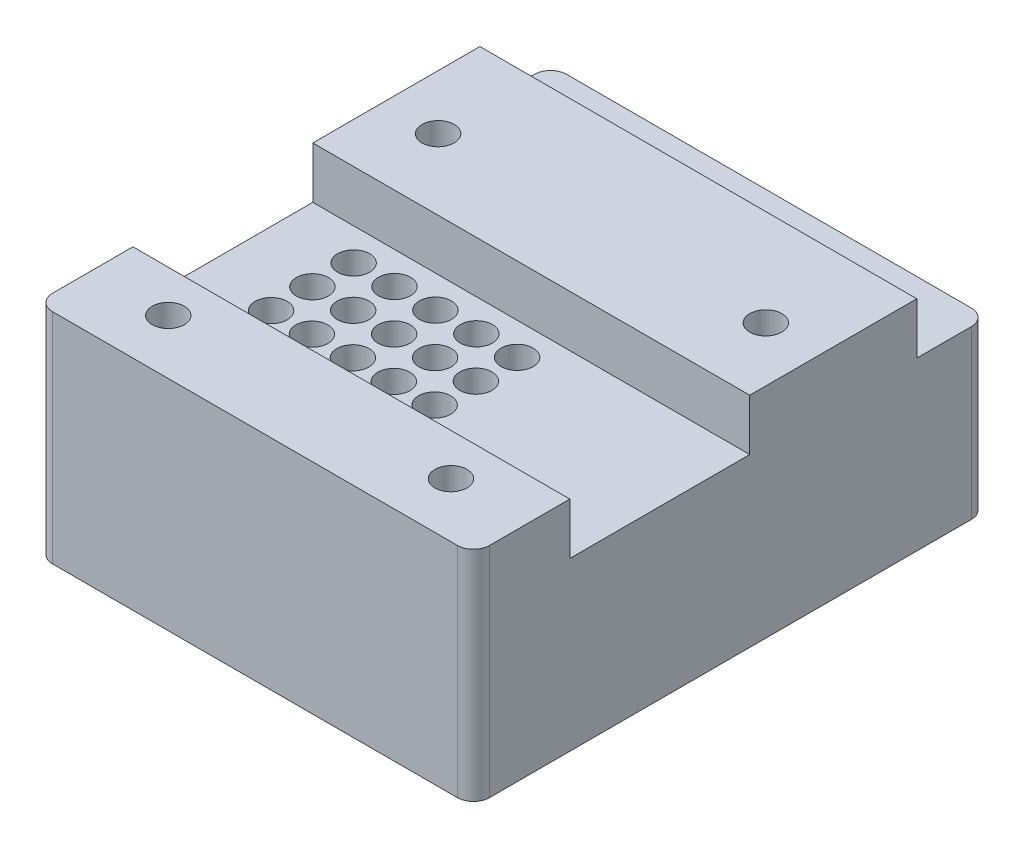
SolidWorks part; units mm, degrees
ref_plane "Front Plane" through (0, 0, 0) normal (0, 0, 1) x (1, 0, 0)
ref_plane "Top Plane" through (0, 0, 0) normal (0, 1, 0) x (1, 0, 0)
ref_plane "Right Plane" through (0, 0, 0) normal (1, 0, 0) x (0, 0, -1)
sketch "Sketch1" plane through (0, 0, 0) normal (0, 1, 0) x (1, 0, 0)
  line L1 (0, 0) -> (68, 0)
  line L2 (0, 0) -> (0, -70)
  line L3 (0, -70) -> (68, -70)
  line L4 (68, 0) -> (68, -70)
  dimension "D1" = 70
  dimension "D2" = 68
extrude "Boss-Extrude2" add sketch "Sketch1" along normal blind 4 contours L2 L1 L4 L3
sketch "Sketch2" plane through (0, 0, 0) normal (0, -1, 0) x (-1, 0, 0)
  line L1 (-34, 0) -> (-34, -70)
  line L2 (0, 0) -> (-68, 0) construction
  line L3 (0, -70) -> (-68, -70) construction
  line L4 (-68, -11) -> (0, -11)
  line L5 (-68, 0) -> (-68, -70) construction
  line L6 (0, 0) -> (0, -70) construction
  line L8 (-54.5, -11) -> (-68, -11)
  line L9 (-54.5, -11) -> (-54.5, -16)
  line L10 (-54.5, -16) -> (-68, -16)
  line L11 (-68, -11) -> (-68, -16)
  line L12 (-13.5, -11) -> (0, -11)
  line L13 (-13.5, -11) -> (-13.5, -16)
  line L14 (-13.5, -16) -> (0, -16)
  line L15 (0, -11) -> (0, -16)
  point P16 (-54.5, -11)
  point P17 (-13.5, -11)
  line M3 (0, -70) -> (0, 0)
  dimension "D1" = 11
  dimension "D2" = 20.5
  dimension "D3" = 20.5
  dimension "D4" = 5
  dimension "D5" = 5
extrude "Boss-Extrude4" add sketch "Sketch2" along normal blind 22 contours L13 L14 L4 M3 | L9 L8 L11 L10
sketch "Sketch3" plane through (0, 0, 11) normal (0, 0, -1) x (-1, 0, 0)
  line L0 (0, 0) -> (-68, 0) construction
  line L1 (-54.5, -22) -> (-54.5, 0) construction
  line L2 (-54.5, 0) -> (-68, 0) construction
  circle A0 centre (-59.07, -14.83) radius 2
  circle A1 centre (-59.07, -4.71) radius 2
  circle A2 centre (-8.93, -14.83) radius 2
  circle A3 centre (-8.93, -4.71) radius 2
  dimension "D1" = 4
  dimension "D2" = 4
  dimension "D3" = 4
  dimension "D4" = 4
  dimension "D5" = 4.71
  dimension "D6" = 4.57
  dimension "D7" = 4.57
  dimension "D8" = 14.83
extrude "Cut-Extrude1" cut sketch "Sketch3" against normal blind 10
sketch "Sketch4" plane through (0, 0, 0) normal (0, -1, 0) x (-1, 0, 0)
  line L0 (0, -42) -> (-68, -42)
  line L1 (0, -16) -> (0, -70) construction
  line L2 (-68, -16) -> (-68, -70) construction
  line L3 (-13.5, -16) -> (0, -16) construction
  line L5 (0, -42) -> (-5, -42)
  line L6 (0, -42) -> (0, -67.69)
  line L7 (0, -67.69) -> (-5, -67.69)
  line L8 (-5, -42) -> (-5, -67.69)
  line L9 (-43.15, -42) -> (-48.15, -42)
  line L10 (-43.15, -42) -> (-43.15, -67.69)
  line L11 (-43.15, -67.69) -> (-48.15, -67.69)
  line L12 (-48.15, -42) -> (-48.15, -67.69)
  line M13 (0, -70) -> (0, -16)
  dimension "D1" = 26
  dimension "D2" = 25.69
  dimension "D3" = 5
  dimension "D4" = 5
  dimension "D5" = 48.15
extrude "Boss-Extrude5" add sketch "Sketch4" along normal blind 15 contours L0 L8 L7 M13 | L0 L12 L11 L10
sketch "Sketch5" plane through (0, -15, 0) normal (0, -1, 0) x (-1, 0, 0)
  line L0 (0, -42) -> (-5, -42) construction
  line L1 (0, -67.69) -> (0, -42) construction
  line L3 (0, -67.69) -> (-5, -67.69) construction
  line L4 (-43.15, -67.69) -> (-48.15, -67.69) construction
  line L5 (-48.15, -42) -> (-48.15, -67.69) construction
  line L6 (-43.15, -42) -> (-48.15, -42) construction
  circle A0 centre (-2.3, -65.24) radius 1.3
  circle A1 centre (-2.3, -44.45) radius 1.3
  circle A2 centre (-45.85, -65.24) radius 1.3
  circle A3 centre (-45.85, -44.45) radius 1.3
  dimension "D1" = 2.6
  dimension "D2" = 2.6
  dimension "D3" = 2.6
  dimension "D4" = 2.6
  dimension "D5" = 2.45
  dimension "D7" = 2.3
  dimension "D8" = 2.45
  dimension "D9" = 2.45
  dimension "D10" = 2.3
  dimension "D11" = 2.45
  dimension "D12" = 2.3
  dimension "D6" = 2.3
extrude "Cut-Extrude2" cut sketch "Sketch5" against normal blind 6
sketch "Sketch6" plane through (0, 0, 70) normal (0, 0, 1) x (1, 0, 0)
  line L1 (0, 4) -> (68, 4)
  line L2 (0, 4) -> (0, 0)
  line L3 (0, 0) -> (68, 0)
  line L4 (68, 4) -> (68, 0)
extrude "Boss-Extrude6" add sketch "Sketch6" along normal blind 10
sketch "Sketch7" plane through (0, 0, 0) normal (0, -1, 0) x (-1, 0, 0)
  line L0 (0, -42) -> (-5, -42) construction
  line L1 (0, -16) -> (-3, -16)
  line L2 (0, -16) -> (0, -42)
  line L3 (0, -42) -> (-3, -42)
  line L4 (-3, -16) -> (-3, -42)
  line L10 (-54.5, -16) -> (-68, -16) construction
  line L19 (-54.5, -11) -> (-68, -11) construction
  line L20 (-65, -11) -> (-68, -11)
  line L21 (-65, -11) -> (-65, 0)
  line L22 (-65, 0) -> (-68, 0)
  line L23 (-68, -11) -> (-68, 0)
  line L24 (0, 0) -> (-68, 0) construction
  line L25 (0, -11) -> (-3, -11)
  line L26 (0, -11) -> (0, 0)
  line L27 (0, 0) -> (-3, 0)
  line L28 (-3, -11) -> (-3, 0)
  line L29 (0, -67.69) -> (-3, -67.69)
  line L30 (-3, 0) -> (-15.1638, 0)
  line L31 (-3, 0) -> (-3, -3)
  line L32 (-3, -3) -> (-15.1638, -3)
  line L33 (-15.1638, 0) -> (-15.1638, -3)
  line L34 (-65, 0) -> (-47.6978, 0)
  line L35 (-65, 0) -> (-65, -3)
  line L36 (-65, -3) -> (-47.6978, -3)
  line L37 (-47.6978, 0) -> (-47.6978, -3)
  line L38 (-3, -77) -> (-59, -77)
  line L39 (-59, -16) -> (-68, -16)
  line L40 (-68, -80) -> (0, -80)
  line L41 (0, -67.69) -> (-3, -67.69)
  line L42 (0, -67.69) -> (-3, -67.69)
  line L43 (-3, -77) -> (-3, -67.69)
  line L44 (0, -67.69) -> (0, -80)
  line L45 (0, -80) -> (-68, -80)
  line L46 (-68, -80) -> (-68, -16)
  line L47 (-59, -16) -> (-59, -77)
  line L48 (0, -67.69) -> (0, -80)
  line M28 (-54.5, -16) -> (-68, -16)
  line M29 (-68, -16) -> (-68, -80)
  line M30 (-68, -80) -> (0, -80)
  line M31 (0, -80) -> (0, -67.69)
  line M32 (0, -67.69) -> (-5, -67.69)
  dimension "D1" = 3
  dimension "D2" = 3
  dimension "D3" = 3
  dimension "D7" = 3
  dimension "D8" = 3
extrude "Boss-Extrude7" add sketch "Sketch7" along normal blind 22 contours L47 L43 L38 M28 M29 M30 M31 M32
sketch "Sketch8" plane through (0, 0, 0) normal (0, -1, 0) x (-1, 0, 0)
  line L0 (-13.5, -16) -> (0, -16) construction
  line L1 (0, -42) -> (-3, -42)
  line L2 (0, -42) -> (0, -16)
  line L3 (0, -16) -> (-3, -16)
  line L4 (-3, -42) -> (-3, -16)
  dimension "D1" = 3
extrude "Boss-Extrude8" add sketch "Sketch8" along normal blind 22
sketch "Sketch9" plane through (0, 0, 0) normal (0, -1, 0) x (1, 0, 0)
  line L5 (68, 11) -> (68, 0)
  line L21 (65, 3) -> (65, 11)
  line L22 (65, 11) -> (68, 11)
  line L23 (0, 11) -> (0, 0)
  line L27 (3, 3) -> (3, 11)
  line L28 (3, 11) -> (0, 11)
  line L29 (3, 3) -> (3, 0)
  line L30 (0, 0) -> (68, 0) construction
  line L31 (3, 0) -> (0, 0)
  line L32 (65, 3) -> (65, 0)
  line L33 (65, 0) -> (68, 0)
  dimension "D3" = 3
extrude "Boss-Extrude9" add sketch "Sketch9" along normal blind 22 contours L27 L28 L23 L31 L29 | L21 L22 L5 L33 L32
sketch "Sketch12" plane through (0, -22, 0) normal (0, -1, 0) x (-1, 0, 0)
  line L0 (-3, -16) -> (-3, -42) construction
  line L1 (0, -42) -> (-3, -42)
  line L2 (0, -42) -> (0, -41)
  line L3 (0, -41) -> (-3, -41)
  line L4 (-3, -42) -> (-3, -41)
  line L5 (-3, -77) -> (-3, -67.69) construction
  line L6 (0, -67.69) -> (-3, -67.69)
  line L7 (0, -67.69) -> (0, -68.69)
  line L8 (0, -68.69) -> (-3, -68.69)
  line L9 (-3, -67.69) -> (-3, -68.69)
  dimension "D1" = 1
  dimension "D2" = 1
extrude "Cut-Extrude5" cut sketch "Sketch12" against normal blind 7
sketch "Sketch13" plane through (0, 4, 0) normal (0, 1, 0) x (1, 0, 0)
  line L0 (68, -11) -> (0, -11)
  line L1 (68, 0) -> (68, -80) construction
  line L2 (0, 0) -> (0, -80) construction
  line L3 (0, 0) -> (68, 0) construction
  line L4 (68, -80) -> (0, -80) construction
  line L5 (68, -11) -> (0, -11)
  line L6 (68, -11) -> (68, -37)
  line L7 (68, -37) -> (0, -37)
  line L8 (0, -11) -> (0, -37)
  line L9 (68, -65) -> (0, -65)
  line L10 (68, -65) -> (68, -80)
  line L11 (68, -80) -> (0, -80)
  line L12 (0, -65) -> (0, -80)
  line M10 (68, -80) -> (68, 0)
  line M14 (0, 0) -> (0, -80)
  dimension "D1" = 11
  dimension "D2" = 26
  dimension "D3" = 0
  dimension "D4" = 15
extrude "Boss-Extrude12" add sketch "Sketch13" along normal blind 8 contours L7 L0 M10 M14 | L11 L9 M10 M14
sketch "Sketch19" plane through (0, -22, 0) normal (0, -1, 0) x (-1, 0, 0)
  line L0 (-3, -77) -> (-59, -77) construction
  line L1 (-59, -16) -> (-65, -16)
  line L2 (-59, -16) -> (-59, -77)
  line L3 (-59, -77) -> (-65, -77)
  line L4 (-65, -16) -> (-65, -77)
  dimension "D1" = 0
extrude "Cut-Extrude8" cut sketch "Sketch19" against normal blind 22
sketch "Sketch20" plane through (0, 0, 0) normal (0, -1, 0) x (1, 0, 0)
  line L0 (3, 16) -> (3, 42) construction
  line L1 (3, 16) -> (6, 16)
  line L2 (3, 16) -> (3, 19)
  line L3 (3, 19) -> (6, 19)
  line L4 (6, 16) -> (6, 19)
  line L5 (65, 16) -> (62, 16)
  line L6 (65, 16) -> (65, 19)
  line L7 (65, 19) -> (62, 19)
  line L8 (62, 16) -> (62, 19)
  dimension "D1" = 3
  dimension "D2" = 3
  dimension "D3" = 3
  dimension "D4" = 3
extrude "Boss-Extrude13" add sketch "Sketch20" along normal blind 22
sketch "Sketch21" plane through (0, 0, 0) normal (0, -1, 0) x (-1, 0, 0)
  line L0 (-68, -80) -> (0, -80) construction
  line L3 (0, -80) -> (0, -68.69) construction
  line L4 (-68, 0) -> (-68, -80) construction
  line L5 (-54.5, -16) -> (-62, -16) construction
  line L6 (0, -41) -> (0, 0) construction
  circle A0 centre (-12, -71.5) radius 5
  circle A4 centre (-56, -71.5) radius 5
  circle A5 centre (-59.5, -26) radius 5
  circle A6 centre (-8.5, -26) radius 5
  circle A7 centre (-8.5, -26) radius 2.5
  circle A8 centre (-12, -71.5) radius 2.5
  circle A9 centre (-56, -71.5) radius 2.5
  circle A10 centre (-59.5, -26) radius 2.5
  dimension "D1" = 10
  dimension "D2" = 8.5
  dimension "D6" = 10
  dimension "D7" = 8.5
  dimension "D8" = 5
  dimension "D9" = 5
  dimension "D10" = 5
  dimension "D11" = 5
  dimension "D3" = 12
  dimension "D4" = 8.5
  dimension "D5" = 12
extrude "Cut-Extrude9" cut sketch "Sketch21" against normal blind 22 contours A7 | A8 | A9 | A10
sketch "Sketch22" plane through (0, 0, 0) normal (0, -1, 0) x (-1, 0, 0)
  circle A0 centre (-12, -71.5) radius 5.0043
  circle A1 centre (-8.5, -26) radius 5.004
  circle A2 centre (-59.5, -26) radius 4.995
  circle A3 centre (-56, -71.5) radius 4.9983
extrude "Cut-Extrude10" cut sketch "Sketch22" against normal blind 6
sketch "Sketch24" plane through (0, 0, 0) normal (0, -1, 0) x (-1, 0, 0)
  line L1 (-3, -77) -> (-6, -77)
  line L2 (-3, -77) -> (-3, -74)
  line L3 (-3, -74) -> (-6, -74)
  line L4 (-6, -77) -> (-6, -74)
  line L5 (-65, -77) -> (-62, -77)
  line L6 (-65, -77) -> (-65, -74)
  line L7 (-65, -74) -> (-62, -74)
  line L8 (-62, -77) -> (-62, -74)
  dimension "D1" = 3
  dimension "D2" = 3
  dimension "D3" = 3
  dimension "D4" = 3
extrude "Boss-Extrude14" add sketch "Sketch24" along normal blind 22
sketch "Sketch26" plane through (0, -22, 0) normal (0, -1, 0) x (-1, 0, 0)
  line L0 (-68, 0) -> (-68, -80) construction
  line L1 (-68, -80) -> (0, -80) construction
  line L2 (0, -80) -> (0, -68.69) construction
  line L3 (-3, 0) -> (-65, 0) construction
  line L4 (-3, 0) -> (0, 0) construction
  line L5 (0, -41) -> (0, 0) construction
  circle A0 centre (-65, -77) radius 1.2
  circle A1 centre (-3, -77) radius 1.2
  circle A2 centre (-65, -16) radius 1.2
  circle A3 centre (-3, -16) radius 1.2
  dimension "D1" = 2.4
  dimension "D2" = 3
  dimension "D3" = 3
  dimension "D4" = 3
  dimension "D5" = 3
  dimension "D8" = 16
  dimension "D10" = 2.4
  dimension "D11" = 2.4
  dimension "D12" = 2.4
  dimension "D6" = 3
  dimension "D7" = 16
  dimension "D9" = 3
extrude "Cut-Extrude11" cut sketch "Sketch26" against normal blind 5
sketch "Sketch27" plane through (0, 0, 0) normal (0, -1, 0) x (-1, 0, 0)
  line L2 (-43.15, -42) -> (-43.15, -67.69)
  line L3 (-43.15, -67.69) -> (-5, -67.69)
  line L4 (-5, -42) -> (-5, -67.69)
  line L10 (-5, -42) -> (-5, -54.845)
  line L11 (-5, -54.845) -> (-5, -42)
  line L13 (-5, -54.845) -> (-5, -67.69)
  circle A0 centre (-11.35, -48.4225) radius 2.5
  circle A1 centre (-11.35, -54.845) radius 2.5
  circle A2 centre (-11.35, -61.2675) radius 2.5
  circle A3 centre (-17.7, -61.2675) radius 2.5
  circle A4 centre (-17.7, -54.845) radius 2.5
  circle A5 centre (-17.7, -48.4225) radius 2.5
  circle A6 centre (-24.075, -61.2675) radius 2.5
  circle A7 centre (-24.075, -54.845) radius 2.5
  circle A8 centre (-24.075, -48.4225) radius 2.5
  circle A9 centre (-30.45, -61.2675) radius 2.5
  circle A10 centre (-30.45, -54.845) radius 2.5
  circle A11 centre (-30.45, -48.4225) radius 2.5
  circle A12 centre (-36.8, -61.2675) radius 2.5
  circle A13 centre (-36.8, -54.845) radius 2.5
  circle A14 centre (-36.8, -48.4225) radius 2.5
  circle A15 centre (-11.35, -42) radius 2.5
  circle A16 centre (-17.7, -42) radius 2.5
  circle A17 centre (-24.075, -42) radius 2.5
  circle A18 centre (-30.45, -42) radius 2.5
  circle A19 centre (-36.8, -42) radius 2.5
  dimension "D2" = 38.15
extrude "Cut-Extrude13" cut sketch "Sketch27" against normal blind 10 contours A19 | A18 | A17 | A16 | A15 | A0 | A5 | A8 | A11 | A14 | A13 | A12 | A10 | A9 | A7 | A6 | A4 | A3 | A1 | A2
fillet "Fillet2" radius 2.5 4 edges at (0, -5, 80) (0, -9, 0) (68, -5, 80) (68, -9, 0)
